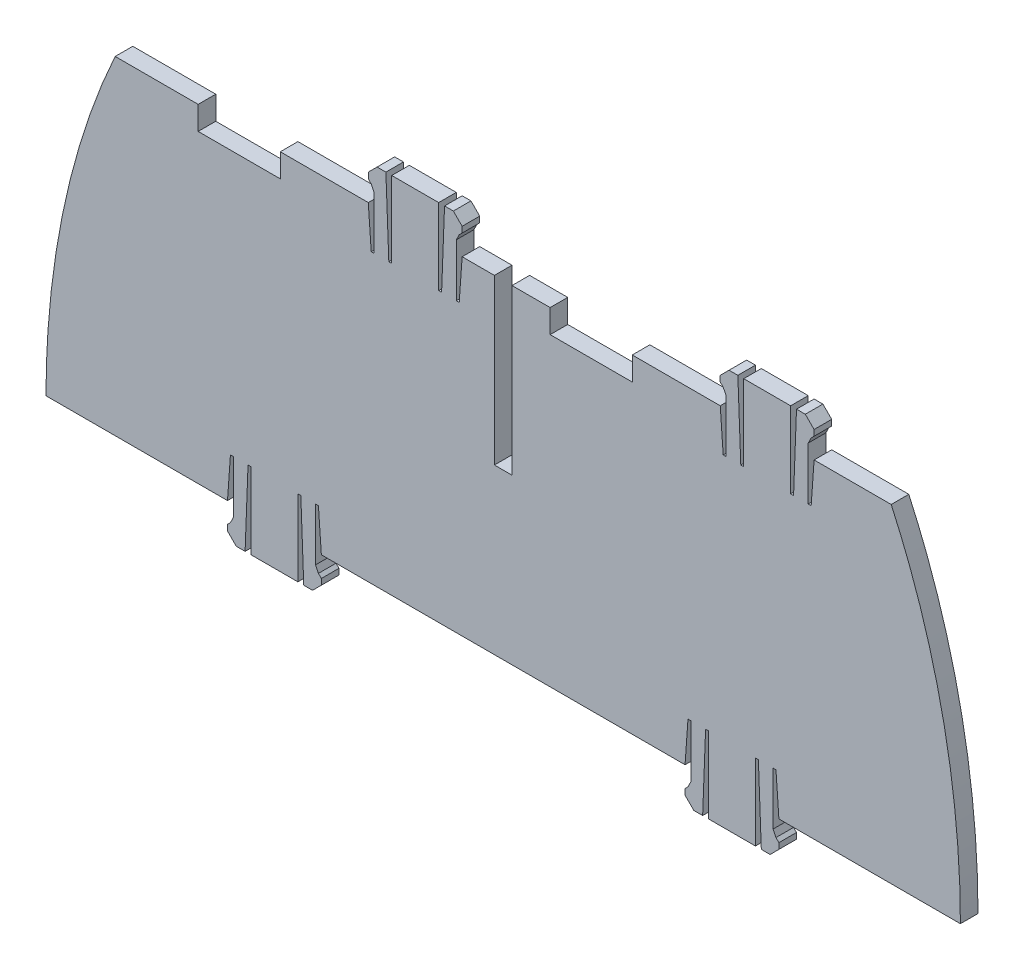
SolidWorks part; units mm, degrees
ref_plane "Front Plane" through (0, 0, 0) normal (0, 0, 1) x (1, 0, 0)
ref_plane "Top Plane" through (0, 0, 0) normal (0, 1, 0) x (1, 0, 0)
ref_plane "Right Plane" through (0, 0, 0) normal (1, 0, 0) x (0, 0, -1)
sketch "Sketch1" plane through (0, 0, 0) normal (0, 0, 1) x (1, 0, 0)
  line L0 (-39, 0) -> (-8, 0)
  line L1 (-39, 0) -> (-39, 56) construction
  line L2 (27.145, 56) -> (14, 56)
  line L3 (-39, 0) -> (-70, 0)
  line L4 (-86, 0) -> (-116.94, 0)
  line L5 (-70, 0) -> (-70.5, 7.0022)
  line L6 (-70.5, 7.0022) -> (-71, 7.0022)
  line L7 (-71, 7.0022) -> (-71, -1.9978)
  line L8 (-71, -1.9978) -> (-70.5, -2.9978)
  line L9 (-70.5, -2.9978) -> (-70, -3.4978)
  line L10 (-70, -3.4978) -> (-70, -4.4978)
  line L11 (-70, -4.4978) -> (-71.5, -5.9978)
  line L12 (-71.5, -5.9978) -> (-73, -5.9978)
  line L13 (-73, -5.9978) -> (-73.5, 7.0022)
  line L14 (-73.5, 7.0022) -> (-74, 7.0022)
  line L15 (-74, 7.0022) -> (-74, -5.9978)
  line L16 (-78, 0) -> (-78, -5.7386) construction
  line L17 (-82, 7.0022) -> (-82, -5.9978)
  line L18 (-82.5, 7.0022) -> (-82, 7.0022)
  line L19 (-83, -5.9978) -> (-82.5, 7.0022)
  line L20 (-84.5, -5.9978) -> (-83, -5.9978)
  line L21 (-86, -4.4978) -> (-84.5, -5.9978)
  line L22 (-86, -3.4978) -> (-86, -4.4978)
  line L23 (-85.5, -2.9978) -> (-86, -3.4978)
  line L24 (-85, -1.9978) -> (-85.5, -2.9978)
  line L25 (-85, 7.0022) -> (-85, -1.9978)
  line L26 (-85.5, 7.0022) -> (-85, 7.0022)
  line L27 (-86, 0) -> (-85.5, 7.0022)
  line L28 (-74, -5.9978) -> (-82, -5.9978)
  line L29 (8, 0) -> (7.5, 7.0022)
  line L30 (7.5, 7.0022) -> (7, 7.0022)
  line L31 (7, 7.0022) -> (7, -1.9978)
  line L32 (7, -1.9978) -> (7.5, -2.9978)
  line L33 (7.5, -2.9978) -> (8, -3.4978)
  line L34 (8, -3.4978) -> (8, -4.4978)
  line L35 (8, -4.4978) -> (6.5, -5.9978)
  line L36 (6.5, -5.9978) -> (5, -5.9978)
  line L37 (5, -5.9978) -> (4.5, 7.0022)
  line L38 (4.5, 7.0022) -> (4, 7.0022)
  line L39 (4, 7.0022) -> (4, -5.9978)
  line L40 (0, 0) -> (0, -5.7386) construction
  line L41 (-4, 7.0022) -> (-4, -5.9978)
  line L42 (-4.5, 7.0022) -> (-4, 7.0022)
  line L43 (-5, -5.9978) -> (-4.5, 7.0022)
  line L44 (-6.5, -5.9978) -> (-5, -5.9978)
  line L45 (-8, -4.4978) -> (-6.5, -5.9978)
  line L46 (-8, -3.4978) -> (-8, -4.4978)
  line L47 (-7.5, -2.9978) -> (-8, -3.4978)
  line L48 (-7, -1.9978) -> (-7.5, -2.9978)
  line L49 (-7, 7.0022) -> (-7, -1.9978)
  line L50 (-7.5, 7.0022) -> (-7, 7.0022)
  line L51 (-8, 0) -> (-7.5, 7.0022)
  line L52 (4, -5.9978) -> (-4, -5.9978)
  line L53 (8, 0) -> (38.94, 0)
  line L54 (-62, 56) -> (-61.5, 48.9978)
  line L55 (-61.5, 48.9978) -> (-61, 48.9978)
  line L56 (-61, 48.9978) -> (-61, 57.9978)
  line L57 (-61, 57.9978) -> (-61.5, 58.9978)
  line L58 (-61.5, 58.9978) -> (-62, 59.4978)
  line L59 (-62, 59.4978) -> (-62, 60.4978)
  line L60 (-62, 60.4978) -> (-60.5, 61.9978)
  line L61 (-60.5, 61.9978) -> (-59, 61.9978)
  line L62 (-59, 61.9978) -> (-58.5, 48.9978)
  line L63 (-58.5, 48.9978) -> (-58, 48.9978)
  line L64 (-58, 48.9978) -> (-58, 61.9978)
  line L65 (-54, 56) -> (-54, 61.7386) construction
  line L66 (-50, 48.9978) -> (-50, 61.9978)
  line L67 (-49.5, 48.9978) -> (-50, 48.9978)
  line L68 (-49, 61.9978) -> (-49.5, 48.9978)
  line L69 (-47.5, 61.9978) -> (-49, 61.9978)
  line L70 (-46, 60.4978) -> (-47.5, 61.9978)
  line L71 (-46, 59.4978) -> (-46, 60.4978)
  line L72 (-46.5, 58.9978) -> (-46, 59.4978)
  line L73 (-47, 57.9978) -> (-46.5, 58.9978)
  line L74 (-47, 48.9978) -> (-47, 57.9978)
  line L75 (-46.5, 48.9978) -> (-47, 48.9978)
  line L76 (-46, 56) -> (-46.5, 48.9978)
  line L77 (-58, 61.9978) -> (-50, 61.9978)
  line L78 (-62, 56) -> (-105.145, 56)
  line L79 (-2, 56) -> (-1.5, 48.9978)
  line L80 (-1.5, 48.9978) -> (-1, 48.9978)
  line L81 (-1, 48.9978) -> (-1, 57.9978)
  line L82 (-1, 57.9978) -> (-1.5, 58.9978)
  line L83 (-1.5, 58.9978) -> (-2, 59.4978)
  line L84 (-2, 59.4978) -> (-2, 60.4978)
  line L85 (-2, 60.4978) -> (-0.5, 61.9978)
  line L86 (-0.5, 61.9978) -> (1, 61.9978)
  line L87 (1, 61.9978) -> (1.5, 48.9978)
  line L88 (1.5, 48.9978) -> (2, 48.9978)
  line L89 (2, 48.9978) -> (2, 61.9978)
  line L90 (6, 56) -> (6, 61.7386) construction
  line L91 (10, 48.9978) -> (10, 61.9978)
  line L92 (10.5, 48.9978) -> (10, 48.9978)
  line L93 (11, 61.9978) -> (10.5, 48.9978)
  line L94 (12.5, 61.9978) -> (11, 61.9978)
  line L95 (14, 60.4978) -> (12.5, 61.9978)
  line L96 (14, 59.4978) -> (14, 60.4978)
  line L97 (13.5, 58.9978) -> (14, 59.4978)
  line L98 (13, 57.9978) -> (13.5, 58.9978)
  line L99 (13, 48.9978) -> (13, 57.9978)
  line L100 (13.5, 48.9978) -> (13, 48.9978)
  line L101 (14, 56) -> (13.5, 48.9978)
  line L102 (2, 61.9978) -> (10, 61.9978)
  line L103 (-2, 56) -> (-46, 56)
  line L104 (-105.145, 56) -> (-39, 0) construction
  ellipse E0 centre (-39, 0) end of major axis (-39, -105.8742) minor radius 77.94 (-105.145, 56) -> (-116.94, 0) ccw
  ellipse E1 centre (-39, 0) end of major axis (-39, -105.8742) minor radius 77.94 (38.94, 0) -> (27.145, 56) ccw
  point P4 (0, 0)
  point P9 (-39, 56)
  point P17 (-78, 0)
  point P19 (-70, 0)
  point P23 (-86, 0)
  point P24 (-86, 0)
  point P51 (-7.97, 0)
  point P52 (8, 0)
  point P79 (-54, 56)
  point P80 (-62, 56)
  point P81 (-46, 56)
  point P82 (-46, 56)
  point P89 (-78, -5.9978)
  point P112 (6, 56)
  point P113 (-2, 56)
  point P114 (14, 56)
  point P115 (14, 56)
  dimension "D1" = 155.88
  dimension "D2" = 56
  dimension "D3" = 132.29
  dimension "D4" = 31
  dimension "D5" = 30.94
  dimension "D6" = 8
  dimension "D7" = 0.5
  dimension "D8" = 9
  dimension "D9" = 0.5
  dimension "D10" = 1
  dimension "D11" = 0.5
  dimension "D12" = 0.5
  dimension "D13" = 1
  dimension "D14" = 1.5
  dimension "D15" = 1.5
  dimension "D16" = 0.5
  dimension "D17" = 0.5
  dimension "D18" = 13
  dimension "D19" = 7.0022
  dimension "D20" = 0.5
  dimension "D21" = 1.5
  dimension "D22" = 13
  dimension "D23" = 39
  dimension "D24" = 47
  dimension "D25" = 5.7386
  dimension "D26" = 0.5
  dimension "D27" = 9
  dimension "D28" = 0.5
  dimension "D29" = 1
  dimension "D30" = 0.5
  dimension "D31" = 0.5
  dimension "D32" = 1
  dimension "D33" = 1.5
  dimension "D34" = 1.5
  dimension "D35" = 0.5
  dimension "D36" = 0.5
  dimension "D37" = 13
  dimension "D38" = 7.0022
  dimension "D39" = 0.5
  dimension "D40" = 1.5
  dimension "D41" = 13
  dimension "D42" = 31
  dimension "D43" = 39
  dimension "D44" = 5.9978
  dimension "D45" = 15
  dimension "D46" = 8
  dimension "D47" = 0.5
  dimension "D48" = 9
  dimension "D49" = 0.5
  dimension "D50" = 1
  dimension "D51" = 0.5
  dimension "D52" = 0.5
  dimension "D53" = 1
  dimension "D54" = 1.5
  dimension "D55" = 1.5
  dimension "D56" = 0.5
  dimension "D57" = 0.5
  dimension "D58" = 13
  dimension "D59" = 7.0022
  dimension "D60" = 0.5
  dimension "D61" = 1.5
  dimension "D62" = 13
  dimension "D63" = 8
  dimension "D64" = 43.145
  dimension "D65" = 7
  dimension "D66" = 45
  dimension "D67" = 8
  dimension "D68" = 0.5
  dimension "D69" = 9
  dimension "D70" = 0.5
  dimension "D71" = 1
  dimension "D72" = 0.5
  dimension "D73" = 0.5
  dimension "D74" = 1
  dimension "D75" = 1.5
  dimension "D76" = 1.5
  dimension "D77" = 0.5
  dimension "D78" = 0.5
  dimension "D79" = 13
  dimension "D80" = 7.0022
  dimension "D81" = 0.5
  dimension "D82" = 1.5
  dimension "D83" = 13
  dimension "D84" = 44
  dimension "D85" = 13.145
  dimension "D86" = 86.667
extrude "Boss-Extrude1" add sketch "Sketch1" along normal blind 3
sketch "Sketch9" plane through (0, 0, 3) normal (0, 0, 1) x (1, 0, 0)
  line L0 (27.145, 56) -> (14, 56) construction
  line L1 (-31, 52) -> (-17, 52)
  line L2 (-31, 52) -> (-31, 56)
  line L3 (-31, 56) -> (-17, 56)
  line L4 (-17, 52) -> (-17, 56)
  line L5 (-31, 52) -> (-17, 56) construction
  line L6 (-31, 56) -> (-17, 52) construction
  line L8 (-91, 52) -> (-77, 52)
  line L9 (-91, 52) -> (-91, 56)
  line L10 (-91, 56) -> (-77, 56)
  line L11 (-77, 52) -> (-77, 56)
  line L12 (-91, 52) -> (-77, 56) construction
  line L13 (-91, 56) -> (-77, 52) construction
  point P0 (-24, 54)
  point P8 (-84, 54)
  dimension "D1" = 4
  dimension "D2" = 14
  dimension "D3" = 15
  dimension "D4" = 4
  dimension "D5" = 14
  dimension "D6" = 15
extrude "Cut-Extrude3" cut sketch "Sketch9" against normal through all
sketch "Sketch10" plane through (0, 0, 3) normal (0, 0, 1) x (1, 0, 0)
sketch "Sketch11" plane through (0, 0, 3) normal (0, 0, 1) x (1, 0, 0)
  line L0 (-40.5, 56) -> (-40.5, 28)
  line L2 (-31, 56) -> (-46, 56) construction
  line L3 (-40.5, 28) -> (-37.5, 28)
  line L4 (-37.5, 28) -> (-37.5, 56)
  dimension "D1" = 28
  dimension "D2" = 3
  dimension "D3" = 6.5
extrude "Cut-Extrude4" cut sketch "Sketch11" against normal blind 3 and the other way through all
sketch "Sketch12" plane through (0, 0, 3) normal (0, 0, 1) x (1, 0, 0)
  text T0 "HY2b" font "Century Gothic" height in points 20
  dimension "D1" = 93.1211
  dimension "D2" = 43.3106
